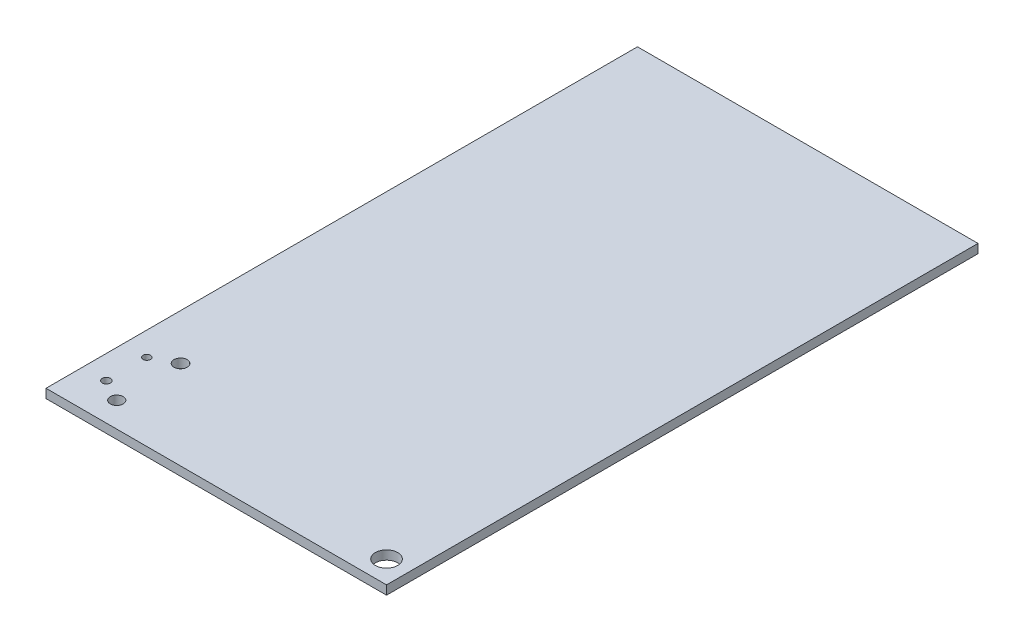
SolidWorks part; units mm, degrees
ref_plane "Front Plane" through (0, 0, 0) normal (0, 0, 1) x (1, 0, 0)
ref_plane "Top Plane" through (0, 0, 0) normal (0, 1, 0) x (1, 0, 0)
ref_plane "Right Plane" through (0, 0, 0) normal (1, 0, 0) x (0, 0, -1)
sketch "Sketch1" plane through (0, 0, 0) normal (0, 1, 0) x (1, 0, 0)
  line L1 (0, 0) -> (38, 0)
  line L2 (0, 0) -> (0, 66)
  line L3 (0, 66) -> (38, 66)
  line L4 (38, 0) -> (38, 66)
  dimension "D1" = 38
  dimension "D2" = 66
extrude "Boss-Extrude1" add sketch "Sketch1" along normal blind 1
sketch "Sketch2" plane through (0, 1, 0) normal (0, 1, 0) x (1, 0, 0)
  line L0 (0, 0) -> (38, 0) construction
  line L1 (38, 0) -> (38, 66) construction
  circle A0 centre (35.5, 2.5) radius 1.25
  dimension "D3" = 2.5
  dimension "D1" = 2.5
  dimension "D2" = 2.5
extrude "Cut-Extrude1" cut sketch "Sketch2" against normal through all
sketch "Sketch3" plane through (0, 1, 0) normal (0, 1, 0) x (1, 0, 0)
  circle A0 centre (2.638, 4.0988) radius 0.4568
  circle A1 centre (2.638, 8.6133) radius 0.41
  circle A2 centre (5.1076, 9.91) radius 0.7399
  circle A3 centre (5.1076, 2.7852) radius 0.7163
extrude "Cut-Extrude2" cut sketch "Sketch3" against normal through all
